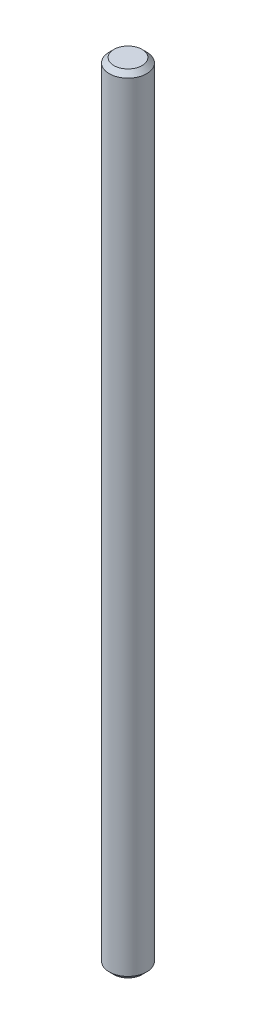
SolidWorks part; units mm, degrees
ref_plane "Front Plane" through (0, 0, 0) normal (0, 0, 1) x (1, 0, 0)
ref_plane "Top Plane" through (0, 0, 0) normal (0, 1, 0) x (1, 0, 0)
ref_plane "Right Plane" through (0, 0, 0) normal (1, 0, 0) x (0, 0, -1)
sketch "Sketch2" plane through (0, 0, 0) normal (0, 1, 0) x (1, 0, 0)
  circle A0 centre (0, 0) radius 2
  dimension "D1" = 4
extrude "Boss-Extrude1" add sketch "Sketch2" along normal blind 84
chamfer "Chamfer1" distance 0.5 angle 45 2 edges at (0, 0, 2) (0, 84, 2)
